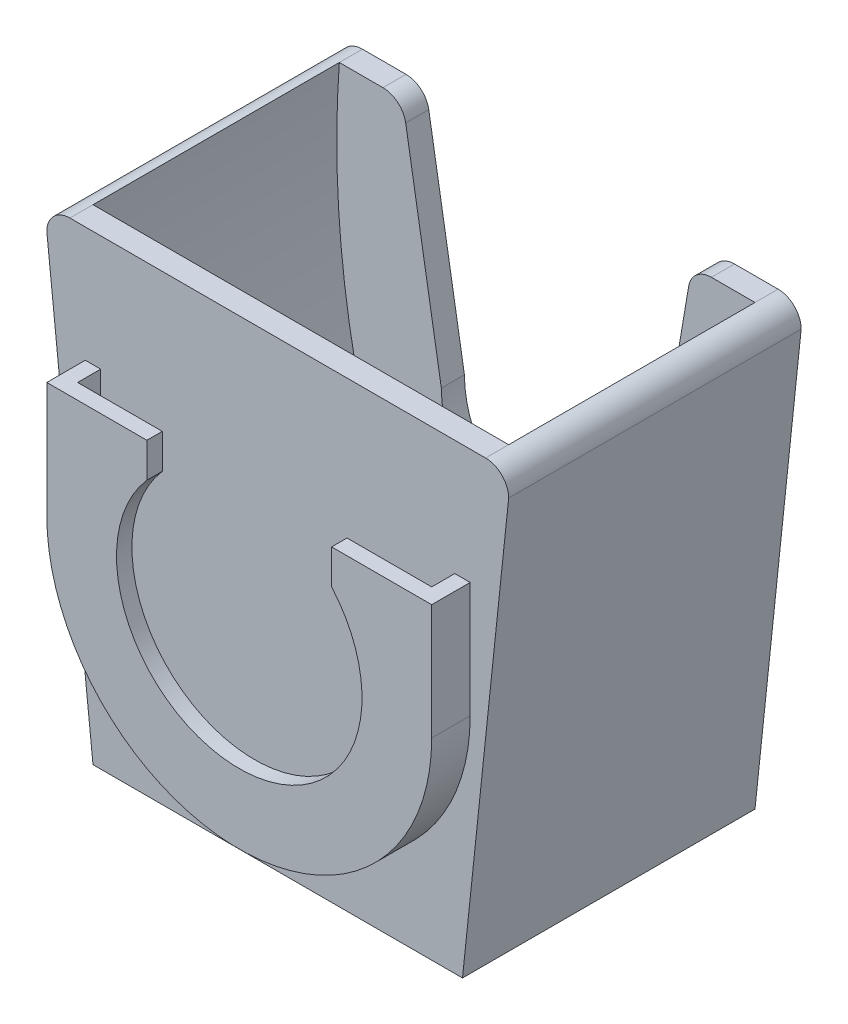
SolidWorks part; units mm, degrees
ref_plane "Alzado" through (0, 0, 0) normal (0, 0, 1) x (1, 0, 0)
ref_plane "Planta" through (0, 0, 0) normal (0, 1, 0) x (1, 0, 0)
ref_plane "Vista lateral" through (0, 0, 0) normal (1, 0, 0) x (0, 0, -1)
sketch "Croquis1" plane through (0, 0, 0) normal (0, 0, 1) x (1, 0, 0)
  line L0 (-27, 30) -> (-21.3363, 30)
  line L3 (-24, -30) -> (24, -30)
  line L5 (-30, 30) -> (24.5714, -24.5714) construction
  line L6 (-30, -30) -> (-29.1213, -29.1213) construction
  line L7 (-18.3779, 27.4979) -> (-13.75, 0)
  line L8 (0, 81.1392) -> (0, -77.9874) construction
  line L9 (18.3779, 27.4979) -> (13.75, 0)
  line L10 (21.3363, 30) -> (27, 30)
  line L11 (30, 27) -> (24, -30)
  line L12 (-30, 27) -> (-24, -30)
  line L13 (-24.5714, -24.5714) -> (30, 30) construction
  circle A0 centre (0, 0) radius 13.75 construction
  arc A1 (-13.75, 0) -> (13.75, 0) centre (0, 0) ccw
  arc A2 (-27, 30) -> (-30, 27) centre (-27, 27) ccw
  arc A3 (-21.3363, 30) -> (-18.3779, 27.4979) centre (-21.3363, 27) cw
  arc A6 (18.3779, 27.4979) -> (21.3363, 30) centre (21.3363, 27) cw
  arc A7 (27, 30) -> (30, 27) centre (27, 27) cw
  point P0 (0, 0)
  point P20 (-18.799, 30)
  point P29 (18.799, 30)
  dimension "D3" = 27.5
  dimension "D7" = 3
  dimension "D8" = 3
  dimension "D1" = 60
  dimension "D2" = 60
  dimension "D4" = 30
  dimension "D9" = 57
  dimension "D10" = 24
  dimension "D11" = 24
extrude "Saliente-Extruir5" add sketch "Croquis1" along normal mid plane 38 contours L10 A7 L11 L3 L12 A2 L0 A3 L7 A1 L9 A6
sketch "Croquis22" plane through (0, 0, 0) normal (0, 0, 1) x (1, 0, 0)
  line L0 (-24, -30) -> (24, -30) construction
  line L1 (0, 38.181) -> (0, -41.2645) construction
  line L2 (16, -30) -> (-16, -30)
  line L3 (30, 27) -> (24, -30) construction
  line L4 (27, 30) -> (18, 30)
  line L5 (18, 30) -> (13.75, 0)
  line L6 (-18, 30) -> (-13.75, 0)
  line L7 (-27, 30) -> (-18, 30)
  arc A0 (27, 30) -> (16, -30) centre (-93.3007, 21.0468) cw
  arc A1 (13.75, 0) -> (-13.75, 0) centre (0, 0) cw
  arc A3 (-27, 30) -> (-16, -30) centre (93.3007, 21.0468) ccw
  point P21 (0, -30)
  dimension "D1" = 122
  dimension "D5" = 13.75
  dimension "D2" = 16
  dimension "D3" = 9
  dimension "D4" = 30
extrude "Cortar-Extruir8" cut sketch "Croquis22" against normal mid plane 32
sketch "Croquis8" plane through (0, 0, 19) normal (0, 0, 1) x (1, 0, 0)
  line L0 (0, 45.2193) -> (0, -44.0281) construction
  line L1 (-21.3363, 30) -> (21.3363, 30)
  line L2 (-21.3363, 30) -> (-21.3363, -14)
  line L3 (-21.3363, -14) -> (0, -13.75)
  line L4 (21.3363, -14) -> (0, -13.75)
  line L5 (21.3363, 30) -> (21.3363, -14)
  arc A0 (-13.75, 0) -> (13.75, 0) centre (0, 0) ccw construction
  point P13 (0, 30)
  dimension "D1" = 44
  dimension "D3" = 42.6726
extrude "Saliente-Extruir8" add sketch "Croquis8" against normal blind 3 contours L4 L3 L2 L1 L5
sketch "Croquis16" plane through (0, 0, 0) normal (0, 1, 0) x (1, 0, 0)
  line L0 (0, -22) -> (0, -24)
  line L1 (-27, -19) -> (27, -19) construction
  line L2 (0, -24) -> (-25, -24)
  line L3 (-25, -24) -> (-25, -19)
  line L9 (-25, -19) -> (-23, -19)
  line L10 (-23, -19) -> (-23, -22)
  line L11 (-23, -22) -> (0, -22)
  dimension "D1" = 25
  dimension "D2" = 2
  dimension "D3" = 2
  dimension "D4" = 3
  dimension "D5" = 23
revolve "Revolución7" add sketch "Croquis16" angle 180 about L0
sketch "Croquis18" plane through (0, 0, 0) normal (0, 1, 0) x (1, 0, 0)
  line L8 (-25, -24) -> (25, -24)
  line L9 (25, -24) -> (25, -19)
  line L10 (25, -19) -> (23, -19)
  line L11 (23, -19) -> (23, -22)
  line L12 (23, -22) -> (-23, -22)
  line L13 (-23, -22) -> (-23, -19)
  line L14 (-23, -19) -> (-25, -19)
  line L15 (-25, -19) -> (-25, -24)
  line L16 (-25, -24) -> (25, -24)
  line L17 (25, -24) -> (25, -19)
  line L18 (25, -19) -> (23, -19)
  line L19 (23, -19) -> (23, -22)
  line L20 (23, -22) -> (-23, -22)
  line L21 (-23, -22) -> (-23, -19)
  line L22 (-23, -19) -> (-25, -19)
  line L23 (-25, -19) -> (-25, -24)
  dimension "D1" = 0
extrude "Saliente-Extruir10" add sketch "Croquis18" along normal blind 15 contours L16 L17 L18 L19 L20 L21 L22 L23
sketch "Croquis19" plane through (0, 0, 0) normal (0, 0, 1) x (1, 0, 0)
  line L0 (0, 38.9693) -> (0, -44.3654) construction
  line L1 (-12, 10.5) -> (-12, 15)
  line L2 (-25, 15) -> (25, 15) construction
  line L3 (-12, 15) -> (12, 15)
  line L4 (12, 10.5) -> (12, 15)
  circle A0 centre (0, 0) radius 15.9452 construction
  arc A1 (-12, 10.5) -> (12, 10.5) centre (0, 0) ccw
  point P13 (0, 15)
  dimension "D1" = 12
  dimension "D3" = 15.9452
  dimension "D2" = 4.5
extrude "Cortar-Extruir7" cut sketch "Croquis19" against normal blind 2 from surface contours A1 L4 L3 L1
